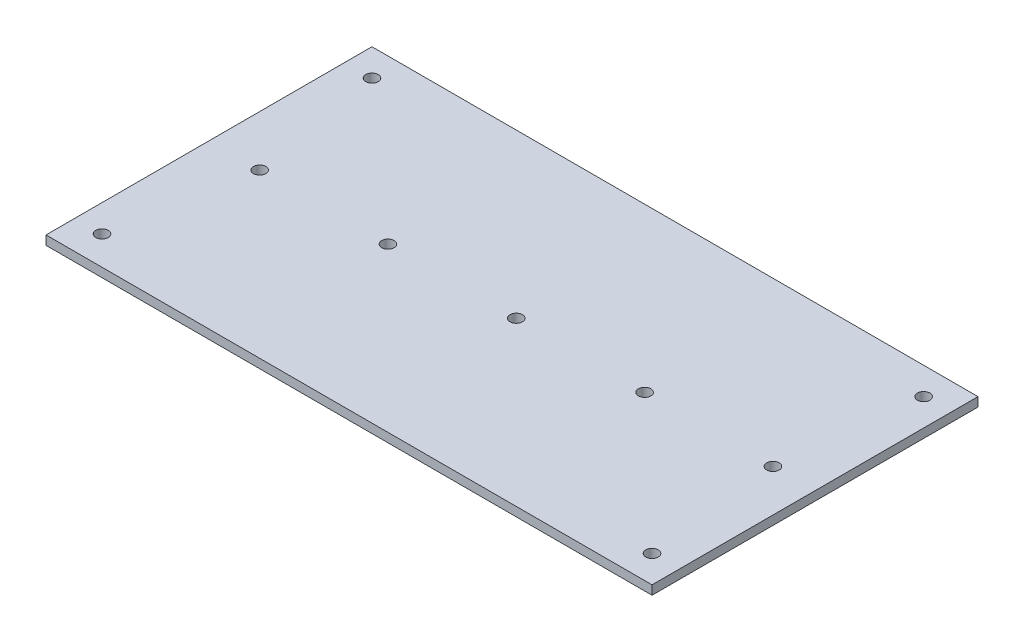
SolidWorks part; units mm, degrees
ref_plane "Front Plane" through (0, 0, 0) normal (0, 0, 1) x (1, 0, 0)
ref_plane "Top Plane" through (0, 0, 0) normal (0, 1, 0) x (1, 0, 0)
ref_plane "Right Plane" through (0, 0, 0) normal (1, 0, 0) x (0, 0, -1)
sketch "Sketch1" plane through (0, 0, 0) normal (0, 1, 0) x (1, 0, 0)
  line L1 (0, 0) -> (425, 0)
  line L2 (0, 0) -> (0, -228.6)
  line L3 (0, -228.6) -> (425, -228.6)
  line L4 (425, 0) -> (425, -228.6)
  dimension "D1" = 425
  dimension "D2" = 228.6
extrude "Base" add sketch "Sketch1" against normal blind 6.35
sketch "Sketch9" plane through (0, 0, 0) normal (0, 1, 0) x (1, 0, 0)
  line L0 (0, -114.3) -> (425, -114.3) construction
  line L1 (0, 0) -> (0, -228.6) construction
  line L2 (425, -228.6) -> (425, 0) construction
  line L3 (35.5, -114.3) -> (125.4998, -114.3) construction
  point P7 (54, -99.3)
  point P21 (304, -129.3)
  point P22 (304, -99.3)
  point P23 (204, -129.3)
  point P24 (204, -99.3)
  point P25 (104, -129.3)
  point P26 (104, -99.3)
  point P27 (154, -99.3)
  point P28 (54, -129.3)
  point P29 (154, -129.3)
  point P30 (35.5, -114.3)
  point P31 (125.4998, -114.3)
  point P33 (215.4996, -114.3)
  point P34 (305.4995, -114.3)
  point P40 (395.4993, -114.3)
  dimension "D2" = 89.9998
  dimension "D3" = 5
  dimension "D1" = 35.5
hole_wizard "Hole for 1/4 Blind Fasteners (B,BS)1" positions "Sketch10" profile "Sketch11" hole size "1/4-20" standard "PEM® Inch" end condition through all
sketch "Sketch10" plane through (0, 0, 0) normal (0, 1, 0) x (1, 0, 0)
  point P42 (35.5, -114.3)
  point P45 (125.4998, -114.3)
  point P48 (215.4996, -114.3)
  point P51 (305.4995, -114.3)
  point P54 (395.4993, -114.3)
sketch "Sketch11" plane through (35.5, 0, 114.3) normal (1, 0, 0) x (0, 0, 1)
  line L0 (0, 0) -> (0, 6.35)
  line L1 (0, 6.35) -> (4.3688, 6.35)
  line L2 (4.3688, 6.35) -> (4.3688, 0)
  line L5 (4.3688, 0) -> (0, 0)
  line L11 (0, -6.35) -> (0, 107.95) construction
  dimension "Thru Hole Dia." = 8.7376
  dimension "Thru Hole Depth" = 6.35
sketch "Sketch12" plane through (0, -6.35, 0) normal (0, -1, 0) x (1, 0, 0)
  line L0 (0, 228.6) -> (425, 228.6) construction
  line L1 (8, 220.6) -> (38, 220.6)
  line L2 (8, 220.6) -> (8, 190.6)
  line L3 (8, 190.6) -> (38, 190.6)
  line L4 (38, 220.6) -> (38, 190.6)
  line L5 (0, 0) -> (0, 228.6) construction
  line L6 (212.5, 228.6) -> (212.5, 0) construction
  line L7 (425, 0) -> (0, 0) construction
  line L8 (0, 114.3) -> (425, 114.3) construction
  line L9 (425, 228.6) -> (425, 0) construction
  line L10 (8, 38) -> (38, 38)
  line L11 (38, 8) -> (38, 38)
  line L12 (8, 8) -> (38, 8)
  line L13 (8, 8) -> (8, 38)
  line L14 (417, 8) -> (417, 38)
  line L15 (417, 8) -> (387, 8)
  line L16 (387, 8) -> (387, 38)
  line L17 (417, 38) -> (387, 38)
  line L18 (417, 190.6) -> (387, 190.6)
  line L19 (387, 220.6) -> (387, 190.6)
  line L20 (417, 220.6) -> (387, 220.6)
  line L21 (417, 220.6) -> (417, 190.6)
  dimension "D1" = 30
  dimension "D2" = 30
extrude "Boss-Extrude1" [suppressed] add sketch "Sketch12" along normal blind 10
sketch "Sketch13" plane through (0, 0, 0) normal (0, 1, 0) x (1, 0, 0)
  line L1 (0, 0) -> (0, -228.6) construction
  line L2 (425, 0) -> (0, 0) construction
  line L3 (425, -228.6) -> (425, 0) construction
  line L4 (0, -228.6) -> (425, -228.6) construction
  point P0 (19.05, -19.05)
  point P1 (405.95, -19.05)
  point P2 (405.95, -209.55)
  point P3 (19.05, -209.55)
  dimension "D1" = 19.05
  dimension "D2" = 19.05
  dimension "D3" = 19.05
  dimension "D4" = 19.05
  dimension "D5" = 19.05
  dimension "D6" = 19.05
  dimension "D7" = 19.05
  dimension "D8" = 19.05
hole_wizard "Hole for 1/4 Blind Fasteners (B,BS)2" positions "Sketch14" profile "Sketch15" hole size "1/4-20" standard "PEM® Inch" end condition through all
sketch "Sketch14" plane through (0, 0, 0) normal (0, 1, 0) x (1, 0, 0)
  point P0 (19.05, -19.05)
  point P3 (19.0341, -208.3655)
  point P7 (405.95, -19.05)
  point P18 (405.95, -209.55)
sketch "Sketch15" plane through (19.05, 0, 19.05) normal (1, 0, 0) x (0, 0, 1)
  line L0 (0, 0) -> (0, 6.35)
  line L1 (0, 6.35) -> (4.3688, 6.35)
  line L2 (4.3688, 6.35) -> (4.3688, 0)
  line L5 (4.3688, 0) -> (0, 0)
  line L11 (0, -6.35) -> (0, 107.95) construction
  dimension "Thru Hole Dia." = 8.7376
  dimension "Thru Hole Depth" = 6.35
